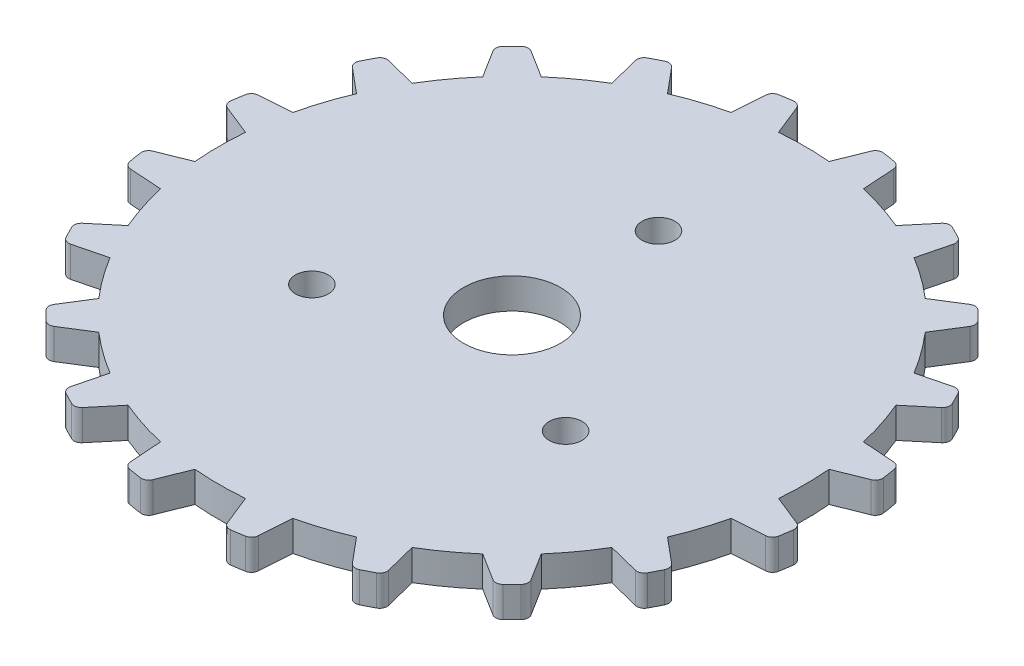
SolidWorks part; units mm, degrees
ref_plane "Front Plane" through (0, 0, 0) normal (0, 0, 1) x (1, 0, 0)
ref_plane "Top Plane" through (0, 0, 0) normal (0, 1, 0) x (1, 0, 0)
ref_plane "Right Plane" through (0, 0, 0) normal (1, 0, 0) x (0, 0, -1)
sketch "Sketch1" plane through (0, 0, 0) normal (0, 1, 0) x (1, 0, 0)
  line L0 (0, 0) -> (0, 28.8903) construction
  line L1 (-3.2322, 26.7985) -> (0, 0)
  line L2 (3.2322, 26.7985) -> (0, 0)
  line L3 (-3.2322, 26.7985) -> (-2.0697, 23.9032)
  line L4 (3.2322, 26.7985) -> (2.0697, 23.9032)
  line L5 (5.2071, 26.4857) -> (5.4181, 23.3729)
  line L6 (11.3552, 24.488) -> (9.3549, 22.0938)
  line L7 (13.1368, 23.5803) -> (12.3756, 20.5547)
  line L8 (18.3667, 19.7806) -> (15.7244, 18.1216)
  line L9 (19.7806, 18.3667) -> (18.1216, 15.7244)
  line L10 (23.5803, 13.1368) -> (20.5547, 12.3756)
  line L11 (24.488, 11.3552) -> (22.0938, 9.3549)
  line L12 (26.4857, 5.2072) -> (23.3729, 5.4181)
  line L13 (26.7985, 3.2322) -> (23.9032, 2.0697)
  line L14 (26.7985, -3.2322) -> (23.9032, -2.0697)
  line L15 (26.4857, -5.2071) -> (23.3729, -5.4181)
  line L16 (24.488, -11.3552) -> (22.0938, -9.3549)
  line L17 (23.5803, -13.1368) -> (20.5547, -12.3756)
  line L18 (19.7806, -18.3667) -> (18.1216, -15.7244)
  line L19 (18.3667, -19.7806) -> (15.7244, -18.1216)
  line L20 (13.1368, -23.5803) -> (12.3756, -20.5547)
  line L21 (11.3552, -24.488) -> (9.3549, -22.0938)
  line L22 (5.2072, -26.4857) -> (5.4181, -23.3729)
  line L23 (3.2322, -26.7985) -> (2.0697, -23.9032)
  line L24 (-3.2322, -26.7985) -> (-2.0697, -23.9032)
  line L25 (-5.2071, -26.4857) -> (-5.4181, -23.3729)
  line L26 (-11.3552, -24.488) -> (-9.3549, -22.0938)
  line L27 (-13.1368, -23.5803) -> (-12.3756, -20.5547)
  line L28 (-18.3667, -19.7806) -> (-15.7244, -18.1216)
  line L29 (-19.7806, -18.3667) -> (-18.1216, -15.7244)
  line L30 (-23.5803, -13.1368) -> (-20.5547, -12.3756)
  line L31 (-24.488, -11.3552) -> (-22.0938, -9.3549)
  line L32 (-26.4857, -5.2072) -> (-23.3729, -5.4181)
  line L33 (-26.7985, -3.2322) -> (-23.9032, -2.0697)
  line L34 (-26.7985, 3.2322) -> (-23.9032, 2.0697)
  line L35 (-26.4857, 5.2071) -> (-23.3729, 5.4181)
  line L36 (-24.488, 11.3552) -> (-22.0938, 9.3549)
  line L37 (-23.5803, 13.1368) -> (-20.5547, 12.3756)
  line L38 (-19.7806, 18.3667) -> (-18.1216, 15.7244)
  line L39 (-18.3667, 19.7806) -> (-15.7244, 18.1216)
  line L40 (-13.1368, 23.5803) -> (-12.3756, 20.5547)
  line L41 (-11.3552, 24.488) -> (-9.3549, 22.0938)
  line L42 (-5.2072, 26.4857) -> (-5.4181, 23.3729)
  line L43 (4.7898, 14.7414) -> (2.7812, 8.5595)
  line L44 (-4.7898, 14.7414) -> (-2.7812, 8.5595)
  line L45 (14.7414, -4.7898) -> (8.5595, -2.7812)
  line L46 (14.7414, 4.7898) -> (8.5595, 2.7812)
  line L47 (-4.7898, -14.7414) -> (-2.7812, -8.5595)
  line L48 (4.7898, -14.7414) -> (2.7812, -8.5595)
  line L49 (-14.7414, 4.7898) -> (-8.5595, 2.7812)
  line L50 (-14.7414, -4.7898) -> (-8.5595, -2.7812)
  circle A0 centre (0, 0) radius 26.9927
  circle A1 centre (0, 0) radius 23.9927
  circle A2 centre (0, 0) radius 9
  circle A3 centre (0, 0) radius 15.5
  point P4 (-3.2322, 26.7985)
  point P7 (3.2322, 26.7985)
  point P9 (-2.0697, 23.9032)
  point P13 (0, 23.9927)
  point P92 (0, 0)
  point P111 (0, 0)
  dimension "D1" = 53.9854
  dimension "D2" = 47.9854
  dimension "D8" = 18
  dimension "D9" = 31
  dimension "D3" = 13.755
  dimension "D4" = 6.877
  dimension "D5" = 15
  dimension "D6" = 15
  dimension "D10" = 18
  dimension "D11" = 18
  dimension "D7" = 20
  dimension "D12" = 4
extrude "Boss-Extrude1" add sketch "Sketch1" against normal blind 2.5 contours A1 L2 L1 | A1 L41 A0 L40 | A1 L1 A0 L42 | A1 L3 L1 | A1 L2 L4 | A1 L5 A0 L2 | A1 L7 A0 L6 | A1 L9 A0 L8 | A1 L11 A0 L10 | A1 L13 A0 L12 | L0 L2 A1 | L1 L0 A1 | A1 L15 A0 L14 | A1 L17 A0 L16 | A1 L19 A0 L18 | A1 L21 A0 L20 | A1 L23 A0 L22 | A1 L25 A0 L24 | A1 L27 A0 L26 | A1 L29 A0 L28 | A1 L31 A0 L30 | A1 L33 A0 L32 | A1 L39 A0 L38 | A1 L37 A0 L36 | A1 L35 A0 L34 | A3
fillet "Fillet1" radius 0.6 40 edges at (-11.3552, -1.25, -24.488) (-18.3667, -1.25, -19.7806) (-26.7985, -1.25, -3.2322) (-13.1368, -1.25, -23.5803) (-19.7806, -1.25, -18.3667) (-23.5803, -1.25, -13.1368) (-24.488, -1.25, -11.3552) (-26.4857, -1.25, -5.2071) (-26.7985, -1.25, 3.2322) (-24.488, -1.25, 11.3552) (-19.7806, -1.25, 18.3667) (-26.4857, -1.25, 5.2072) (-23.5803, -1.25, 13.1368) (-18.3667, -1.25, 19.7806) (-13.1368, -1.25, 23.5803) (-11.3552, -1.25, 24.488) (-5.2071, -1.25, 26.4857) (-3.2322, -1.25, 26.7985) (3.2322, -1.25, 26.7985) (5.2072, -1.25, 26.4857) (11.3552, -1.25, 24.488) (13.1368, -1.25, 23.5803) (18.3667, -1.25, 19.7806) (19.7806, -1.25, 18.3667) (23.5803, -1.25, 13.1368) (24.488, -1.25, 11.3552) (26.4857, -1.25, 5.2071) (26.7985, -1.25, 3.2322) (26.7985, -1.25, -3.2322) (26.4857, -1.25, -5.2072) (24.488, -1.25, -11.3552) (23.5803, -1.25, -13.1368) (19.7806, -1.25, -18.3667) (18.3667, -1.25, -19.7806) (13.1368, -1.25, -23.5803) (11.3552, -1.25, -24.488) (5.2071, -1.25, -26.4857) (3.2322, -1.25, -26.7985) (-5.2072, -1.25, -26.4857) (-3.2322, -1.25, -26.7985)
sketch "Sketch2" plane through (0, -2.5, 0) normal (0, -1, 0) x (1, 0, 0)
  line L0 (14.7414, -4.7898) -> (8.5595, -2.7812) construction
  line L1 (14.7414, 4.7898) -> (8.5595, 2.7812) construction
  line L2 (4.7898, 14.7414) -> (2.7812, 8.5595) construction
  line L3 (-4.7898, 14.7414) -> (-2.7812, 8.5595) construction
  line L4 (-14.7414, 4.7898) -> (-8.5595, 2.7812) construction
  line L5 (-14.7414, -4.7898) -> (-8.5595, -2.7812) construction
  line L6 (-4.7898, -14.7414) -> (-2.7812, -8.5595) construction
  line L7 (4.7898, -14.7414) -> (2.7812, -8.5595) construction
  line L8 (14.7414, -4.7898) -> (8.5595, -2.7812)
  line L9 (14.7414, 4.7898) -> (8.5595, 2.7812)
  line L10 (4.7898, 14.7414) -> (2.7812, 8.5595)
  line L11 (-4.7898, 14.7414) -> (-2.7812, 8.5595)
  line L12 (-14.7414, 4.7898) -> (-8.5595, 2.7812)
  line L13 (-14.7414, -4.7898) -> (-8.5595, -2.7812)
  line L14 (-4.7898, -14.7414) -> (-2.7812, -8.5595)
  line L15 (4.7898, -14.7414) -> (2.7812, -8.5595)
  circle A0 centre (0, 0) radius 9 construction
  circle A1 centre (0, 0) radius 15.5 construction
  circle A2 centre (0, 0) radius 9
  circle A3 centre (0, 0) radius 15.5
extrude "Cut-Extrude1" [suppressed] cut sketch "Sketch2" against normal through all contours L14 A3 L15 A2 | L8 A3 L9 A2 | L10 A3 L11 A2 | L12 A3 L13 A2
sketch "Sketch3" plane through (0, -2.5, 0) normal (0, -1, 0) x (1, 0, 0)
  circle A0 centre (0, 0) radius 2
  dimension "D1" = 4
extrude "Cut-Extrude2" [suppressed] cut sketch "Sketch3" against normal through all
sketch "Sketch4" [suppressed] plane through (0, 0, 0) normal (0, 1, 0) x (1, 0, 0)
  line L0 (0, 0) -> (50.7534, 29.3025) construction
  line L1 (0, 0) -> (0, 45.599) construction
  line L8 (5.8954, 8.0774) -> (8.7636, 12.1737)
  line L9 (9.9429, 1.0668) -> (14.9245, 1.5027)
  line L10 (4.0476, -9.1442) -> (6.1609, -13.6764)
  line L11 (-4.0476, -9.1442) -> (-6.1609, -13.6764)
  line L12 (-9.9429, 1.0668) -> (-14.9245, 1.5027)
  line L13 (-5.8954, 8.0774) -> (-8.7636, 12.1737)
  arc A6 (14.9245, 1.5027) -> (8.7636, 12.1737) centre (0, 0) ccw
  arc A7 (9.9429, 1.0668) -> (5.8954, 8.0774) centre (0, 0) ccw
  arc A8 (-6.1609, -13.6764) -> (6.1609, -13.6764) centre (0, 0) ccw
  arc A9 (-4.0476, -9.1442) -> (4.0476, -9.1442) centre (0, 0) ccw
  arc A10 (-8.7636, 12.1737) -> (-14.9245, 1.5027) centre (0, 0) ccw
  arc A11 (-5.8954, 8.0774) -> (-9.9429, 1.0668) centre (0, 0) ccw
  point P18 (0, 0)
  dimension "D1" = 20
  dimension "D2" = 30
  dimension "D3" = 60
  dimension "D4" = 25
extrude "Cut-Extrude3" [suppressed] cut sketch "Sketch4" against normal blind 10
sketch "Sketch5" plane through (0, 0, 0) normal (0, 1, 0) x (1, 0, 0)
  line L0 (0, 0) -> (0, 34.8888) construction
  circle A0 centre (0, 12) radius 1.35
  circle A1 centre (10.3923, -6) radius 1.35
  circle A2 centre (-10.3923, -6) radius 1.35
  point P11 (0, 0)
  dimension "D1" = 2.7
  dimension "D2" = 12
  dimension "D3" = 3
extrude "Cut-Extrude4" cut sketch "Sketch5" against normal through all
sketch "Sketch6" plane through (0, 0, 0) normal (0, 1, 0) x (1, 0, 0)
  circle A0 centre (0, 0) radius 3.9688
  dimension "D1" = 7.9375
extrude "Cut-Extrude5" cut sketch "Sketch6" against normal through all
